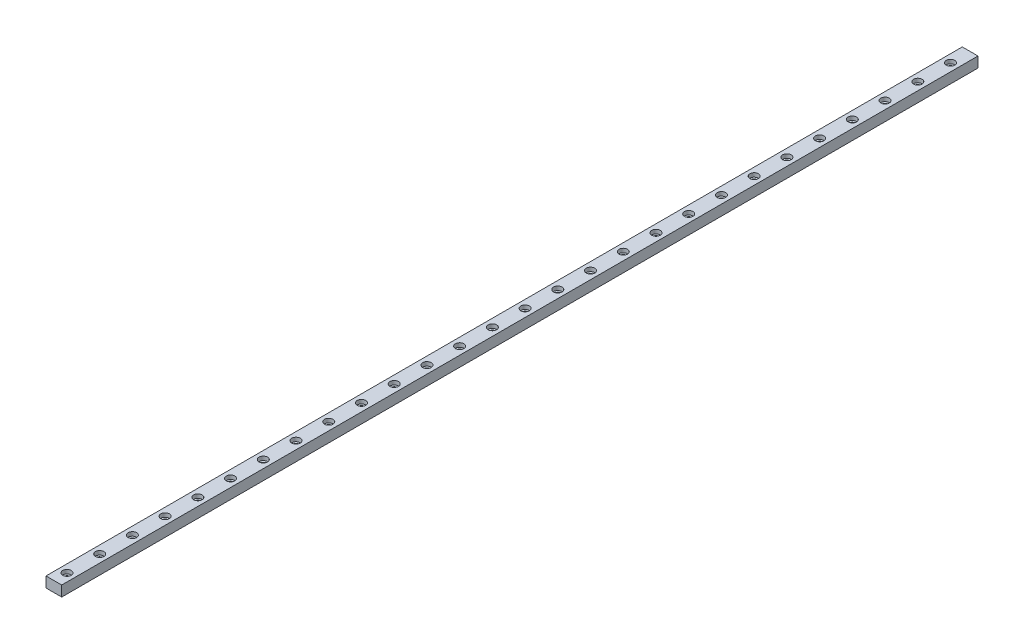
SolidWorks part; units mm, degrees
ref_plane "Front" through (0, 0, 0) normal (0, 0, 1) x (1, 0, 0)
ref_plane "Top" through (0, 0, 0) normal (0, 1, 0) x (1, 0, 0)
ref_plane "Right" through (0, 0, 0) normal (1, 0, 0) x (0, 0, -1)
sketch "Sketch1" plane through (0, 0, 0) normal (0, 0, 1) x (1, 0, 0)
  line L1 (0, 0) -> (12, 0)
  line L2 (0, 0) -> (0, 8)
  line L3 (0, 8) -> (12, 8)
  line L4 (12, 0) -> (12, 8)
  dimension "D1" = 12
  dimension "D2" = 8
extrude "Boss-Extrude1" add sketch "Sketch1" along normal blind 700
hole_wizard "CBORE for M3 SHCS1" positions "Sketch2" profile "Sketch3" counterbore size "M3" standard "ANSI Metric" end condition through all
sketch "Sketch2" plane through (0, 8, 0) normal (0, 1, 0) x (1, 0, 0)
  line L0 (12, -700) -> (0, -700) construction
  point P0 (6, -690)
  point P11 (6, -665)
  point P12 (6, -640)
  point P13 (6, -615)
  point P14 (6, -590)
  point P15 (6, -565)
  point P16 (6, -540)
  point P17 (6, -515)
  point P18 (6, -490)
  point P19 (6, -465)
  point P20 (6, -440)
  point P21 (6, -415)
  point P22 (6, -390)
  point P23 (6, -365)
  point P24 (6, -340)
  point P25 (6, -315)
  point P30 (6, -290)
  point P31 (6, -265)
  point P32 (6, -240)
  point P33 (6, -215)
  point P34 (6, -190)
  point P35 (6, -165)
  point P36 (6, -140)
  point P37 (6, -115)
  point P38 (6, -90)
  point P39 (6, -65)
  point P40 (6, -40)
  point P41 (6, -15)
  dimension "D1" = 10
  dimension "D2" = 28
sketch "Sketch3" plane through (6, 8, 690) normal (1, 0, 0) x (0, 0, 1)
  line L0 (0, 0) -> (0, 8)
  line L1 (0, 8) -> (1.7, 8)
  line L3 (1.7, 8) -> (1.7, 3)
  line L4 (1.7, 3) -> (3.25, 3)
  line L5 (3.25, 3) -> (3.25, 0)
  line L7 (3.25, 0) -> (0, 0)
  line L11 (0, -6.35) -> (0, 107.95) construction
  dimension "Thru Hole Dia." = 3.4
  dimension "Thru Hole Depth" = 8
  dimension "C'Bore Dia." = 6.5
  dimension "C'Bore Depth" = 3
equation "\"length\"=700"
equation "\"D1@Boss-Extrude1\"= \"length\""
